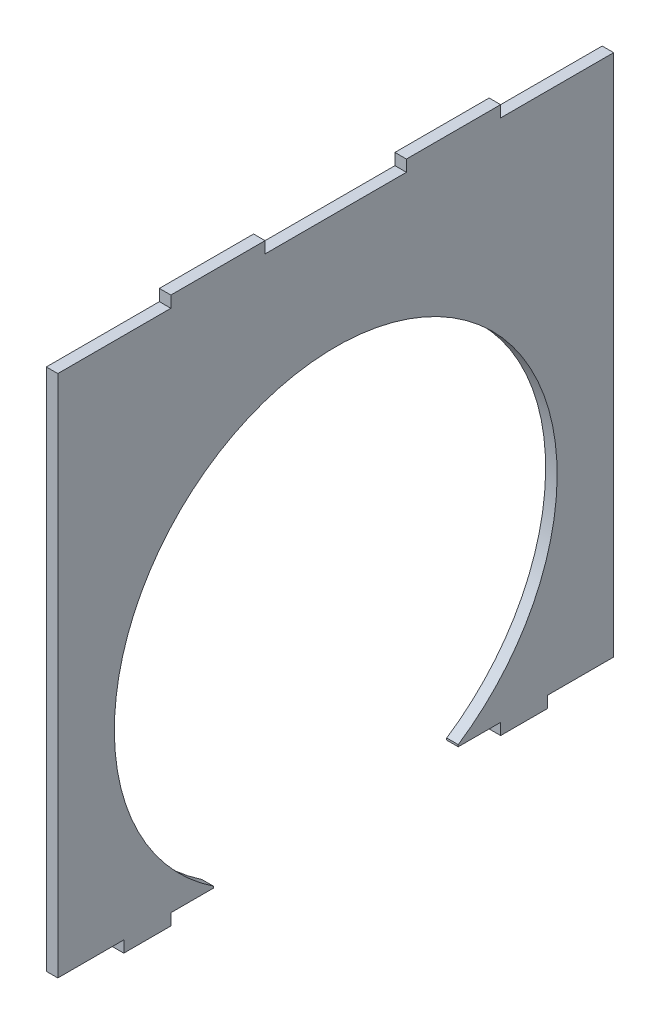
SolidWorks part; units mm, degrees
ref_plane "Alzado" through (0, 0, 0) normal (0, 0, 1) x (1, 0, 0)
ref_plane "Planta" through (0, 0, 0) normal (0, 1, 0) x (1, 0, 0)
ref_plane "Vista lateral" through (0, 0, 0) normal (1, 0, 0) x (0, 0, -1)
sketch "Croquis1" plane through (0, 0, 0) normal (1, 0, 0) x (0, 0, -1)
  line L0 (26, -55.56) -> (26, -55.1535)
  line L1 (-59, -55.56) -> (-45, -55.56)
  line L2 (-59, -55.56) -> (-59, 55.56)
  line L3 (-59, 55.56) -> (-35, 55.56)
  line L4 (59, -55.56) -> (59, 55.56)
  line L5 (-59, -55.56) -> (59, 55.56) construction
  line L6 (-59, 55.56) -> (59, -55.56) construction
  line L7 (26, -55.56) -> (35, -55.56)
  line L8 (-26, -55.56) -> (-26, -55.1535)
  line L9 (0, -63) -> (0, -55.56) construction
  line L10 (0, 0) -> (0, -55.56) construction
  line L11 (0, -55.56) -> (26, -55.56) construction
  line L12 (45, -55.56) -> (59, -55.56)
  line L13 (35, -58) -> (45, -58)
  line L14 (35, -58) -> (35, -55.56)
  line L15 (-35, -58) -> (-35, -55.56)
  line L16 (45, -58) -> (45, -55.56)
  line L17 (35, -58) -> (45, -55.56) construction
  line L18 (35, -55.56) -> (45, -58) construction
  line L19 (-35, -58) -> (-45, -58)
  line L20 (-45, -58) -> (-45, -55.56)
  line L21 (-35, -55.56) -> (-26, -55.56)
  line L22 (-15, 55.56) -> (15, 55.56)
  line L23 (-35, 58) -> (-15, 58)
  line L24 (-35, 58) -> (-35, 55.56)
  line L25 (15, 58) -> (15, 55.56)
  line L26 (-15, 58) -> (-15, 55.56)
  line L27 (-35, 58) -> (-15, 55.56) construction
  line L28 (-35, 55.56) -> (-15, 58) construction
  line L29 (35, 58) -> (35, 55.56)
  line L30 (35, 58) -> (15, 58)
  line L31 (35, 55.56) -> (59, 55.56)
  arc A0 (26, -55.1535) -> (-26, -55.1535) centre (0, -16) ccw
  arc A1 (-26, -55.1535) -> (26, -55.1535) centre (0, -16) ccw construction
  point P0 (0, 0)
  point P15 (40, -56.78)
  point P24 (-25, 56.78)
  dimension "D3" = 94
  dimension "D1" = 111.12
  dimension "D2" = 118
  dimension "D4" = 26
  dimension "D5" = 7.44
  dimension "D6" = 35
  dimension "D7" = 10
  dimension "D8" = 2.44
  dimension "D9" = 15
  dimension "D10" = 20
  dimension "D11" = 2.44
extrude "Saliente-Extruir1" add sketch "Croquis1" along normal blind 2.44
